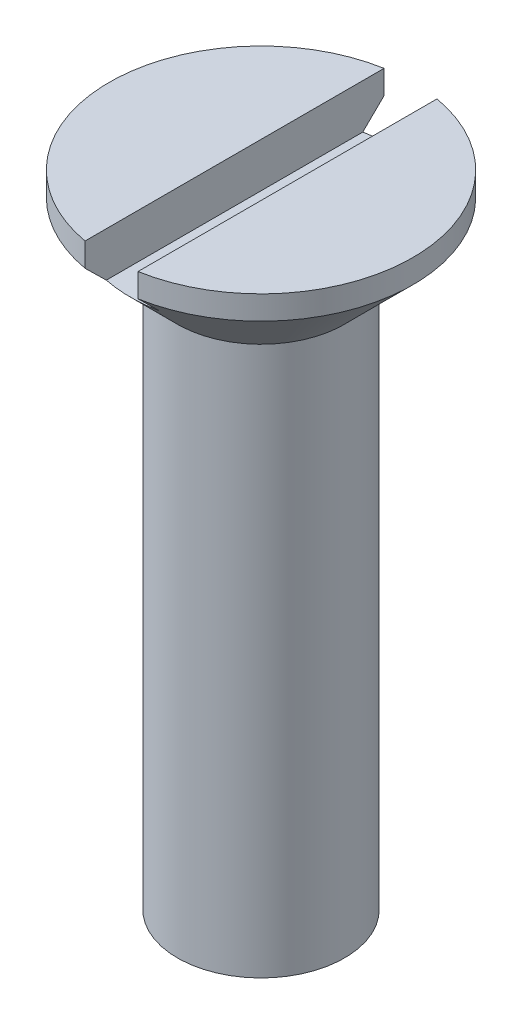
SolidWorks part; units mm, degrees
ref_plane "Front Plane" through (0, 0, 0) normal (0, 0, 1) x (1, 0, 0)
ref_plane "Top Plane" through (0, 0, 0) normal (0, 1, 0) x (1, 0, 0)
ref_plane "Right Plane" through (0, 0, 0) normal (1, 0, 0) x (0, 0, -1)
sketch "Sketch1" plane through (0, 0, 0) normal (0, 0, 1) x (1, 0, 0)
  line L0 (0, 0) -> (3, 1.7321)
  line L1 (3, 1.7321) -> (3, 21.4321)
  line L2 (3, 21.4321) -> (5.45, 23.8821)
  line L3 (5.45, 24.7321) -> (0, 24.7321)
  line L4 (0, 24.7321) -> (0, 0) construction
  line L5 (5.45, 24.7321) -> (5.45, 23.8821)
  line L6 (0, 0) -> (0, 24.7321)
  dimension "D1" = 45
  dimension "D2" = 23
  dimension "D3" = 60
  dimension "D4" = 6
  dimension "D5" = 3.3
  dimension "D6" = 10.9
revolve "Revolve1" add sketch "Sketch1" angle 360 about L4
sketch "Sketch2" plane through (0, 0, 0) normal (0, 0, 1) x (1, 0, 0)
  line L0 (5.45, 24.7321) -> (-5.45, 24.7321) construction
  line L1 (-0.95, 26.3321) -> (0.95, 26.3321)
  line L2 (-0.95, 26.3321) -> (-0.95, 23.1321)
  line L3 (-0.95, 23.1321) -> (0.95, 23.1321)
  line L4 (0.95, 26.3321) -> (0.95, 23.1321)
  line L5 (-0.95, 26.3321) -> (0.95, 23.1321) construction
  line L6 (-0.95, 23.1321) -> (0.95, 26.3321) construction
  point P0 (0, 24.7321)
  dimension "D1" = 1.9
  dimension "D2" = 1.6
extrude "Cut-Extrude1" cut sketch "Sketch2" against normal through all both and the other way through all
